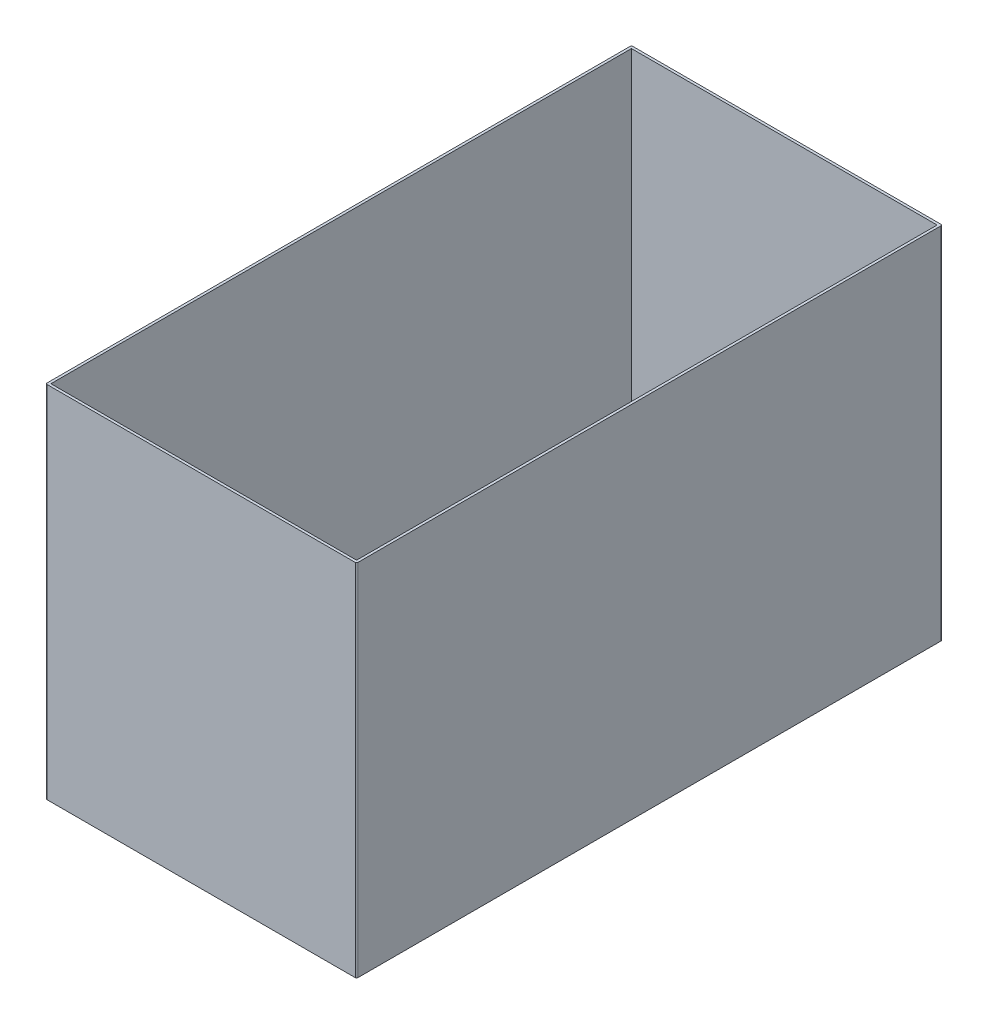
SolidWorks part; units mm, degrees
ref_plane "Front Plane" through (0, 0, 0) normal (0, 0, 1) x (1, 0, 0)
ref_plane "Top Plane" through (0, 0, 0) normal (0, 1, 0) x (1, 0, 0)
ref_plane "Right Plane" through (0, 0, 0) normal (1, 0, 0) x (0, 0, -1)
sketch "Sketch1" plane through (0, 0, 0) normal (0, 1, 0) x (1, 0, 0)
  line L1 (5.95, -11.3) -> (-5.95, -11.3)
  line L2 (5.95, -11.3) -> (5.95, 11.3)
  line L3 (5.95, 11.3) -> (-5.95, 11.3)
  line L4 (-5.95, -11.3) -> (-5.95, 11.3)
  line L5 (5.95, -11.3) -> (-5.95, 11.3) construction
  line L6 (5.95, 11.3) -> (-5.95, -11.3) construction
  point P0 (0, 0)
  dimension "D1" = 11.9
  dimension "D2" = 22.6
extrude "Extrude-Thin1" add sketch "Sketch1" along normal mid plane 14 thin thin type one direction wall 0.1
fillet "Fillet1" radius 0.05 4 edges at (6.05, 0, -11.4) (-6.05, 0, -11.4) (-6.05, 0, 11.4) (6.05, 0, 11.4)
